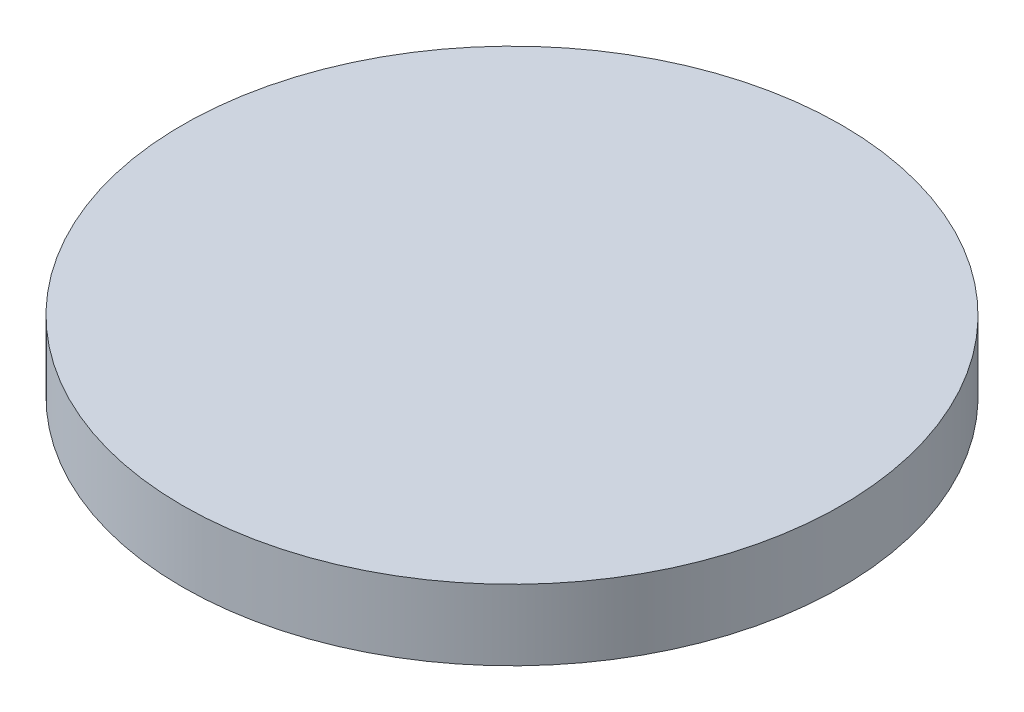
SolidWorks part; units mm, degrees
material "Delrin 2700 NC010, Low Viscosity Acetal Copolymer (SS)"
ref_plane "Front Plane" through (0, 0, 0) normal (0, 0, 1) x (1, 0, 0)
ref_plane "Top Plane" through (0, 0, 0) normal (0, 1, 0) x (1, 0, 0)
ref_plane "Right Plane" through (0, 0, 0) normal (1, 0, 0) x (0, 0, -1)
sketch "Sketch1" plane through (0, 0, 0) normal (0, 1, 0) x (1, 0, 0)
  circle A0 centre (0, 0) radius 3.556
  dimension "D1" = 7.112
extrude "Boss-Extrude1" add sketch "Sketch1" along normal blind 0.762
equation "\"puck_dia\"= 0.28in'FLXLC-A diameter"
equation "\"puck_thick\"= 0.03in'FLXLC-A thickness"
equation "\"sensor_width_space\"= 0.5in'Width from sensor to middle"
equation "\"sensor_length_space\"= 2.4in'Length b/w sensors"
equation "\"divot_depth\"= 0.02in'Divot depth in bottom rubber"
equation "\"divot_dia\"= \"puck_dia\" + 0.005'Divot diameter in bottom rubber"
equation "\"D1@Sketch3\"= \"divot_dia\""
equation "\"D2@Sketch3\"=\"sensor_width_space\""
equation "\"D1@Cut-Extrude2\"=\"divot_depth\""
equation "\"D1@Sketch1\"=\"puck_dia\""
equation "\"D1@Boss-Extrude1\"=\"puck_thick\""
